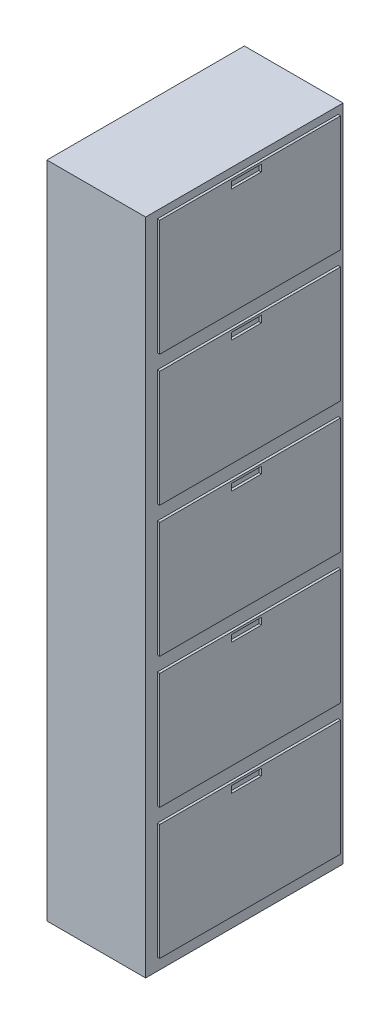
SolidWorks part; units mm, degrees
ref_plane "Front Plane" through (0, 0, 0) normal (0, 0, 1) x (1, 0, 0)
ref_plane "Top Plane" through (0, 0, 0) normal (0, 1, 0) x (1, 0, 0)
ref_plane "Right Plane" through (0, 0, 0) normal (1, 0, 0) x (0, 0, -1)
sketch "Sketch1" plane through (0, 0, 0) normal (0, 0, 1) x (1, 0, 0)
  line L0 (263.062, 4179.9863) -> (-136.938, 4179.9863)
  line L1 (-136.938, 4179.9863) -> (-136.938, 1509.9863)
  line L2 (-136.938, 1509.9863) -> (263.062, 1509.9863)
  line L5 (263.062, 1509.9863) -> (263.062, 4179.9863)
  dimension "D1" = 400
  dimension "D2" = 2670
extrude "Boss-Extrude1" add sketch "Sketch1" along normal blind 800
sketch "Sketch3" plane through (263.062, 0, 0) normal (1, 0, 0) x (0, 0, -1)
  line L0 (-752.8351, 2089.9863) -> (-20, 2089.9863)
  line L1 (-752.8351, 1559.9863) -> (-20, 1559.9863)
  line L2 (-752.8351, 1559.9863) -> (-752.8351, 2029.9863)
  line L3 (-752.8351, 2029.9863) -> (-20, 2029.9863)
  line L4 (-20, 1559.9863) -> (-20, 2029.9863)
  line L5 (-800, 1509.9863) -> (0, 1509.9863) construction
  line L6 (-462.2979, 1993.6554) -> (-341.2251, 1993.6554)
  line L7 (-461.6648, -2274.1108) -> (-340.5919, -2274.1108)
  line L8 (-461.6648, -2274.1108) -> (-461.6648, -2299.9132)
  line L9 (-461.6648, -2299.9132) -> (-340.5919, -2299.9132)
  line L10 (-340.5919, -2274.1108) -> (-340.5919, -2299.9132)
  line L11 (-462.2979, 1993.6554) -> (-462.2979, 2021.1606)
  line L12 (-462.2979, 2021.1606) -> (-341.2251, 2021.1606)
  line L13 (-341.2251, 1993.6554) -> (-341.2251, 2021.1606)
  line L14 (-461.6648, -1727.3383) -> (-340.5919, -1727.3383)
  line L15 (-461.6648, -1753.1407) -> (-340.5919, -1753.1407)
  line L16 (-461.6648, -1727.3383) -> (-461.6648, -1753.1407)
  line L17 (-340.5919, -1727.3383) -> (-340.5919, -1753.1407)
  line L18 (-752.8351, 2089.9863) -> (-752.8351, 2559.9863)
  line L19 (-752.8351, 2559.9863) -> (-20, 2559.9863)
  line L20 (-20, 2089.9863) -> (-20, 2559.9863)
  line L21 (-462.2979, 2523.6554) -> (-341.2251, 2523.6554)
  line L22 (-462.2979, 2523.6554) -> (-462.2979, 2551.1606)
  line L23 (-462.2979, 2551.1606) -> (-341.2251, 2551.1606)
  line L24 (-341.2251, 2523.6554) -> (-341.2251, 2551.1606)
  line L25 (-752.8351, 2619.9863) -> (-20, 2619.9863)
  line L26 (-752.8351, 2619.9863) -> (-752.8351, 3089.9863)
  line L27 (-752.8351, 3089.9863) -> (-20, 3089.9863)
  line L28 (-20, 2619.9863) -> (-20, 3089.9863)
  line L29 (-462.2979, 3053.6554) -> (-341.2251, 3053.6554)
  line L30 (-462.2979, 3053.6554) -> (-462.2979, 3081.1606)
  line L31 (-462.2979, 3081.1606) -> (-341.2251, 3081.1606)
  line L32 (-341.2251, 3053.6554) -> (-341.2251, 3081.1606)
  line L33 (-752.8351, 3149.9863) -> (-20, 3149.9863)
  line L34 (-752.8351, 3149.9863) -> (-752.8351, 3619.9863)
  line L35 (-752.8351, 3619.9863) -> (-20, 3619.9863)
  line L36 (-20, 3149.9863) -> (-20, 3619.9863)
  line L37 (-462.2979, 3583.6554) -> (-341.2251, 3583.6554)
  line L38 (-462.2979, 3583.6554) -> (-462.2979, 3611.1606)
  line L39 (-462.2979, 3611.1606) -> (-341.2251, 3611.1606)
  line L40 (-341.2251, 3583.6554) -> (-341.2251, 3611.1606)
  line L41 (-752.8351, 3679.9863) -> (-20, 3679.9863)
  line L42 (-752.8351, 3679.9863) -> (-752.8351, 4149.9863)
  line L43 (-752.8351, 4149.9863) -> (-20, 4149.9863)
  line L44 (-20, 3679.9863) -> (-20, 4149.9863)
  line L45 (-462.2979, 4113.6554) -> (-341.2251, 4113.6554)
  line L46 (-462.2979, 4113.6554) -> (-462.2979, 4141.1606)
  line L47 (-462.2979, 4141.1606) -> (-341.2251, 4141.1606)
  line L48 (-341.2251, 4113.6554) -> (-341.2251, 4141.1606)
  line L116 (-752.8351, 5934.1662) -> (-752.8351, 6404.1662) [skipped]
  line L117 (-752.8351, 6404.1662) -> (-20, 6404.1662) [skipped]
  line L118 (-20, 5934.1662) -> (-20, 6404.1662) [skipped]
  line L119 (-752.8351, 6480.9387) -> (-20, 6480.9387) [skipped]
  line L120 (-752.8351, 6480.9387) -> (-752.8351, 6950.9387) [skipped]
  line L121 (-752.8351, 6950.9387) -> (-20, 6950.9387) [skipped]
  line L122 (-20, 6480.9387) -> (-20, 6950.9387) [skipped]
  line L123 (-752.8351, 7027.7112) -> (-20, 7027.7112) [skipped]
  line L124 (-752.8351, 7027.7112) -> (-752.8351, 7497.7112) [skipped]
  line L125 (-752.8351, 7497.7112) -> (-20, 7497.7112) [skipped]
  line L126 (-20, 7027.7112) -> (-20, 7497.7112) [skipped]
  line L127 (-752.8351, 7574.4837) -> (-20, 7574.4837) [skipped]
  line L128 (-752.8351, 7574.4837) -> (-752.8351, 8044.4837) [skipped]
  line L129 (-752.8351, 8044.4837) -> (-20, 8044.4837) [skipped]
  line L130 (-20, 7574.4837) -> (-20, 8044.4837) [skipped]
  line L131 (-752.8351, 8121.2562) -> (-20, 8121.2562) [skipped]
  line L132 (-752.8351, 8121.2562) -> (-752.8351, 8591.2562) [skipped]
  line L133 (-752.8351, 8591.2562) -> (-20, 8591.2562) [skipped]
  line L134 (-20, 8121.2562) -> (-20, 8591.2562) [skipped]
  line L135 (-752.8351, 8668.0286) -> (-20, 8668.0286) [skipped]
  line L136 (-752.8351, 8668.0286) -> (-752.8351, 9138.0286) [skipped]
  line L137 (-752.8351, 9138.0286) -> (-20, 9138.0286) [skipped]
  line L138 (-20, 8668.0286) -> (-20, 9138.0286) [skipped]
  line L139 (-752.8351, 5387.3937) -> (-752.8351, 5857.3937) [skipped]
  line L140 (-752.8351, 5857.3937) -> (-20, 5857.3937) [skipped]
  line L141 (-20, 5387.3937) -> (-20, 5857.3937) [skipped]
  line L142 (-752.8351, 5934.1662) -> (-20, 5934.1662) [skipped]
  line L143 (-461.6648, 4833.9315) -> (-340.5919, 4833.9315) [skipped]
  line L144 (-461.6648, 4808.1291) -> (-340.5919, 4808.1291) [skipped]
  line L145 (-461.6648, 4833.9315) -> (-461.6648, 4808.1291) [skipped]
  line L146 (-340.5919, 4833.9315) -> (-340.5919, 4808.1291) [skipped]
  line L147 (-752.8351, 5387.3937) -> (-20, 5387.3937) [skipped]
  line L148 (-461.6648, 4287.1591) -> (-340.5919, 4287.1591) [skipped]
  line L149 (-461.6648, 4261.3567) -> (-340.5919, 4261.3567) [skipped]
  line L150 (-461.6648, 4287.1591) -> (-461.6648, 4261.3567) [skipped]
  line L151 (-340.5919, 4287.1591) -> (-340.5919, 4261.3567) [skipped]
  line L152 (-461.6648, -1180.5658) -> (-340.5919, -1180.5658) [skipped]
  line L153 (-461.6648, -1206.3682) -> (-340.5919, -1206.3682) [skipped]
  line L154 (-461.6648, -1180.5658) -> (-461.6648, -1206.3682) [skipped]
  line L155 (-340.5919, -1180.5658) -> (-340.5919, -1206.3682) [skipped]
  line L156 (-461.6648, -633.7933) -> (-340.5919, -633.7933) [skipped]
  line L157 (-461.6648, -659.5957) -> (-340.5919, -659.5957) [skipped]
  line L158 (-461.6648, -633.7933) -> (-461.6648, -659.5957) [skipped]
  line L159 (-340.5919, -633.7933) -> (-340.5919, -659.5957) [skipped]
  line L160 (-461.6648, -87.0208) -> (-340.5919, -87.0208) [skipped]
  line L161 (-461.6648, -112.8232) -> (-340.5919, -112.8232) [skipped]
  line L162 (-461.6648, -87.0208) -> (-461.6648, -112.8232) [skipped]
  line L163 (-340.5919, -87.0208) -> (-340.5919, -112.8232) [skipped]
  line L164 (-752.8351, 2106.7588) -> (-20, 2106.7588) [skipped]
  line L165 (-752.8351, 2106.7588) -> (-752.8351, 2576.7588) [skipped]
  line L166 (-752.8351, 2576.7588) -> (-20, 2576.7588) [skipped]
  line L167 (-20, 2106.7588) -> (-20, 2576.7588) [skipped]
  line L168 (-752.8351, 2653.5313) -> (-20, 2653.5313) [skipped]
  line L169 (-752.8351, 2653.5313) -> (-752.8351, 3123.5313) [skipped]
  line L170 (-752.8351, 3123.5313) -> (-20, 3123.5313) [skipped]
  line L171 (-20, 2653.5313) -> (-20, 3123.5313) [skipped]
  line L172 (-752.8351, 3200.3038) -> (-20, 3200.3038) [skipped]
  line L173 (-752.8351, 3200.3038) -> (-752.8351, 3670.3038) [skipped]
  line L174 (-752.8351, 3670.3038) -> (-20, 3670.3038) [skipped]
  line L175 (-20, 3200.3038) -> (-20, 3670.3038) [skipped]
  line L176 (-752.8351, 3747.0763) -> (-20, 3747.0763) [skipped]
  line L177 (-752.8351, 3747.0763) -> (-752.8351, 4217.0763) [skipped]
  line L178 (-752.8351, 4217.0763) -> (-20, 4217.0763) [skipped]
  line L179 (-20, 3747.0763) -> (-20, 4217.0763) [skipped]
  line L180 (-752.8351, 4293.8488) -> (-20, 4293.8488) [skipped]
  line L181 (-752.8351, 4293.8488) -> (-752.8351, 4763.8488) [skipped]
  line L182 (-752.8351, 4763.8488) -> (-20, 4763.8488) [skipped]
  line L183 (-20, 4293.8488) -> (-20, 4763.8488) [skipped]
  line L184 (-752.8351, 4840.6212) -> (-20, 4840.6212) [skipped]
  line L185 (-752.8351, 4840.6212) -> (-752.8351, 5310.6212) [skipped]
  line L186 (-752.8351, 5310.6212) -> (-20, 5310.6212) [skipped]
  line L187 (-20, 4840.6212) -> (-20, 5310.6212) [skipped]
  line L188 (-461.6648, 2100.0691) -> (-340.5919, 2100.0691) [skipped]
  line L189 (-461.6648, 2100.0691) -> (-461.6648, 2074.2667) [skipped]
  line L190 (-340.5919, 2100.0691) -> (-340.5919, 2074.2667) [skipped]
  line L191 (-461.6648, 2646.8416) -> (-340.5919, 2646.8416) [skipped]
  line L192 (-461.6648, 2621.0392) -> (-340.5919, 2621.0392) [skipped]
  line L193 (-461.6648, 2646.8416) -> (-461.6648, 2621.0392) [skipped]
  line L194 (-340.5919, 2646.8416) -> (-340.5919, 2621.0392) [skipped]
  line L195 (-461.6648, 3193.6141) -> (-340.5919, 3193.6141) [skipped]
  line L196 (-461.6648, 3167.8117) -> (-340.5919, 3167.8117) [skipped]
  line L197 (-461.6648, 3193.6141) -> (-461.6648, 3167.8117) [skipped]
  line L198 (-340.5919, 3193.6141) -> (-340.5919, 3167.8117) [skipped]
  line L199 (-461.6648, 3740.3866) -> (-340.5919, 3740.3866) [skipped]
  line L200 (-461.6648, 3714.5842) -> (-340.5919, 3714.5842) [skipped]
  line L201 (-461.6648, 3740.3866) -> (-461.6648, 3714.5842) [skipped]
  line L202 (-340.5919, 3740.3866) -> (-340.5919, 3714.5842) [skipped]
  line L203 (-461.6648, 2074.2667) -> (-340.5919, 2074.2667) [skipped]
  line L204 (-461.6648, 459.7517) -> (-340.5919, 459.7517) [skipped]
  line L205 (-461.6648, 433.9492) -> (-340.5919, 433.9492) [skipped]
  line L206 (-461.6648, 459.7517) -> (-461.6648, 433.9492) [skipped]
  line L207 (-340.5919, 459.7517) -> (-340.5919, 433.9492) [skipped]
  line L208 (-461.6648, 1006.5241) -> (-340.5919, 1006.5241) [skipped]
  line L209 (-461.6648, 980.7217) -> (-340.5919, 980.7217) [skipped]
  line L210 (-461.6648, 1006.5241) -> (-461.6648, 980.7217) [skipped]
  line L211 (-340.5919, 1006.5241) -> (-340.5919, 980.7217) [skipped]
  line L212 (-461.6648, 1553.2966) -> (-340.5919, 1553.2966) [skipped]
  line L213 (-461.6648, 1527.4942) -> (-340.5919, 1527.4942) [skipped]
  line L214 (-461.6648, 1553.2966) -> (-461.6648, 1527.4942) [skipped]
  line L215 (-340.5919, 1553.2966) -> (-340.5919, 1527.4942) [skipped]
  dimension "D1" = 470
  dimension "D2" = 5
  dimension "D3" = 50
  dimension "D4" = 14
extrude "Boss-Extrude3" add sketch "Sketch3" along normal blind 10
